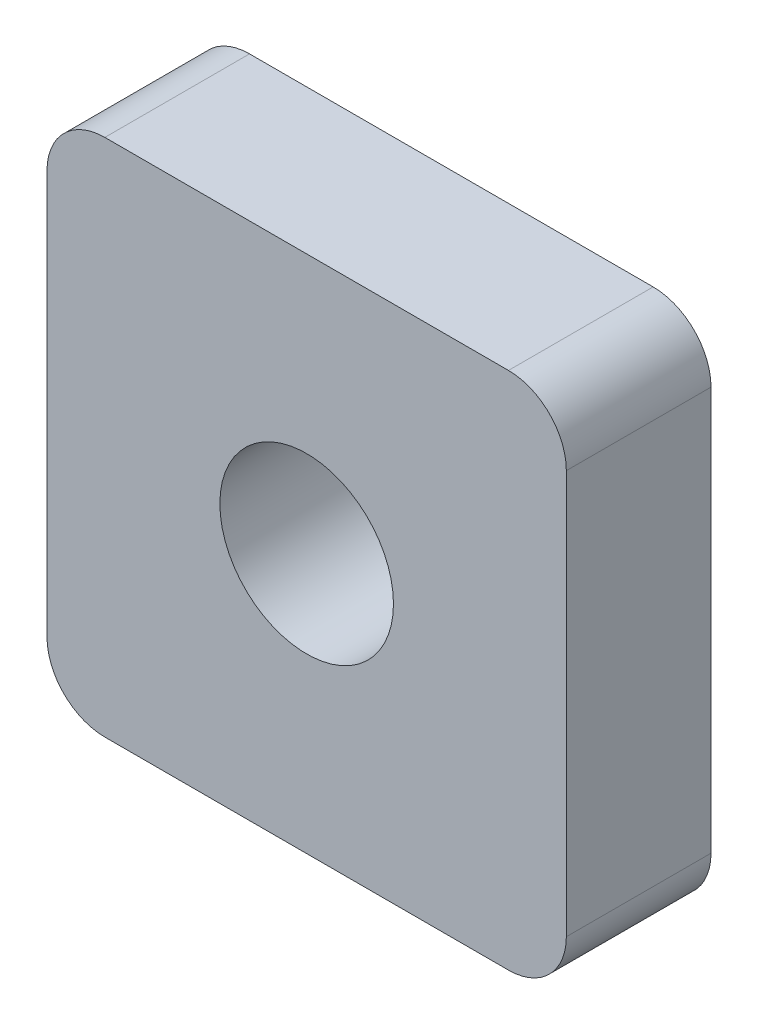
SolidWorks part; units mm, degrees
material "Thornel Mat VMA"
ref_plane "前视基准面" through (0, 0, 0) normal (0, 0, 1) x (1, 0, 0)
ref_plane "上视基准面" through (0, 0, 0) normal (0, 1, 0) x (1, 0, 0)
ref_plane "右视基准面" through (0, 0, 0) normal (1, 0, 0) x (0, 0, -1)
other "Configuration Table"
sketch "草图1" plane through (0, 0, 0) normal (0, 0, 1) x (1, 0, 0)
  line L1 (-8.975, -8.975) -> (8.975, -8.975)
  line L2 (-8.975, -8.975) -> (-8.975, 8.975)
  line L3 (-8.975, 8.975) -> (8.975, 8.975)
  line L4 (8.975, -8.975) -> (8.975, 8.975)
  line L5 (-8.975, -8.975) -> (8.975, 8.975) construction
  line L6 (-8.975, 8.975) -> (8.975, -8.975) construction
  circle A0 centre (0, 0) radius 3
  point P0 (0, 0)
  point P8 (4.8061, 5.8199)
  dimension "D1" = 6
  dimension "D2" = 17.95
extrude "凸台-拉伸1" add sketch "草图1" along normal blind 5
fillet "圆角1" radius 2 4 edges at (8.975, -8.975, 2.5) (-8.975, -8.975, 2.5) (-8.975, 8.975, 2.5) (8.975, 8.975, 2.5)
